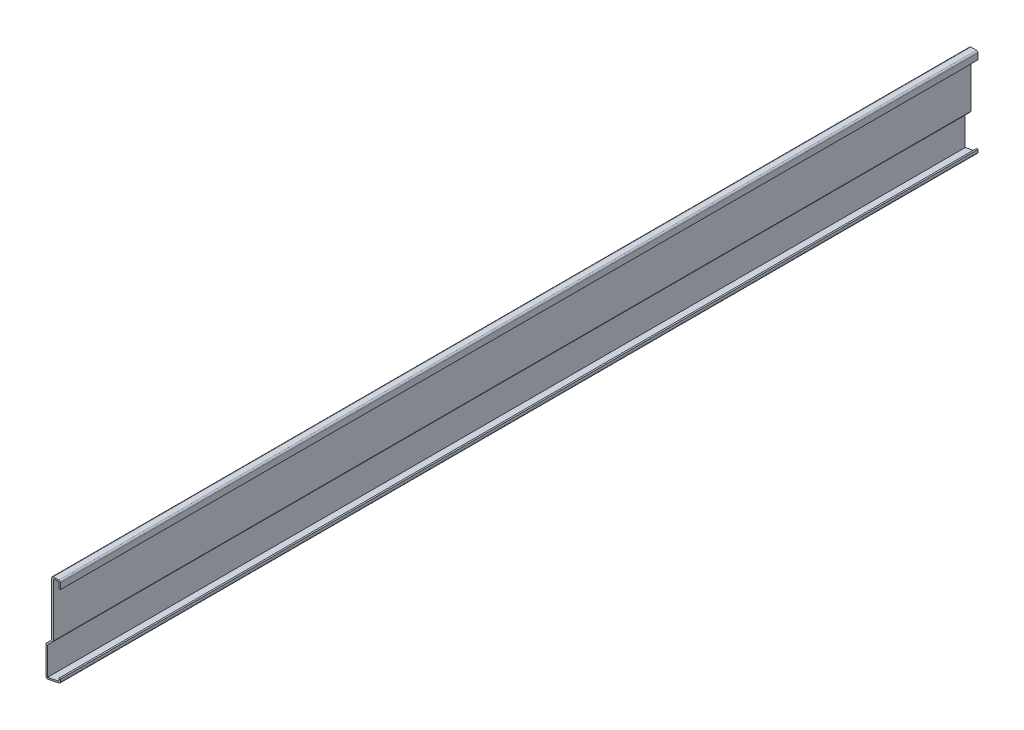
SolidWorks part; units mm, degrees
ref_plane "Front Plane" through (0, 0, 0) normal (0, 0, 1) x (1, 0, 0)
ref_plane "Top Plane" through (0, 0, 0) normal (0, 1, 0) x (1, 0, 0)
ref_plane "Right Plane" through (0, 0, 0) normal (1, 0, 0) x (0, 0, -1)
sketch "Sketch1" plane through (0, 0, 0) normal (0, 0, 1) x (1, 0, 0)
  line L0 (0, 0) -> (0, 76.2) construction
  line L1 (0, 69.85) -> (0, 76.2)
  line L2 (0, 76.2) -> (-7.1438, 76.2)
  line L3 (-7.1438, 76.2) -> (-7.1438, 30.1625)
  line L4 (-7.1438, 30.1625) -> (-11.9063, 25.4)
  line L5 (-11.9063, 25.4) -> (-11.9062, 0)
  line L6 (-11.9062, 0) -> (0, 2.3812)
  line L7 (0, 2.3812) -> (0, 5.5562)
  point P4 (0, 0)
extrude "Extrude-Thin1" add sketch "Sketch1" against normal blind 762 thin thin type one direction reverse wall 1.27
fillet "Fillet1" radius 1.27 6 edges at (0, 2.3812, -381) (-11.9062, 0, -381) (-11.9063, 25.4, -381) (-5.8738, 29.6364, -381) (-7.1438, 76.2, -381) (0, 76.2, -381)
equation "\"D1@Extrude-Thin1\"=\"D9@Sketch1\"*10"
